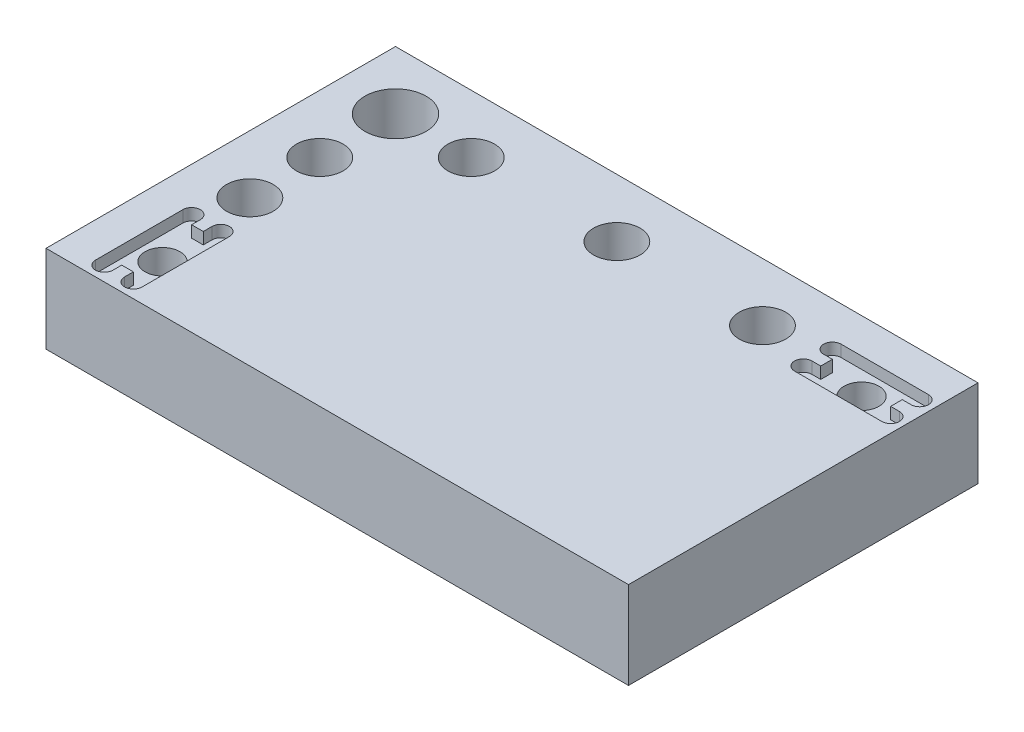
SolidWorks part; units mm, degrees
material "7075-T6, Plate (SS)"
ref_plane "Front Plane" through (0, 0, 0) normal (0, 0, 1) x (1, 0, 0)
ref_plane "Top Plane" through (0, 0, 0) normal (0, 1, 0) x (1, 0, 0)
ref_plane "Right Plane" through (0, 0, 0) normal (1, 0, 0) x (0, 0, -1)
sketch "Sketch1" plane through (0, 0, 0) normal (0, 1, 0) x (1, 0, 0)
  line L1 (-50, -30) -> (50, -30)
  line L2 (-50, -30) -> (-50, 30)
  line L3 (-50, 30) -> (50, 30)
  line L4 (50, -30) -> (50, 30)
  line L5 (-50, -30) -> (50, 30) construction
  line L6 (-50, 30) -> (50, -30) construction
  point P0 (0, 0)
  dimension "D1" = 100
  dimension "D2" = 60
extrude "Boss-Extrude1" add sketch "Sketch1" along normal blind 15
sketch "Sketch4" plane through (0, 15, 0) normal (0, 1, 0) x (1, 0, 0)
  line L0 (-50, 30) -> (-50, -30) construction
  line L1 (50, 30) -> (-50, 30) construction
  circle A0 centre (-40, 20) radius 3
  dimension "D3" = 6
  dimension "D1" = 10
  dimension "D2" = 10
extrude "Cut-Extrude1" cut sketch "Sketch4" against normal up to next
sketch "Sketch5" plane through (0, 15, 0) normal (0, 1, 0) x (1, 0, 0)
  circle A0 centre (-40, 20) radius 5.25
  dimension "D1" = 10.5
extrude "Cut-Extrude2" cut sketch "Sketch5" against normal blind 7.7
sketch "Sketch6" plane through (0, 15, 0) normal (0, 1, 0) x (1, 0, 0)
  line L0 (-50, 30) -> (-50, -30) construction
  line L1 (50, 30) -> (-50, 30) construction
  circle A0 centre (-40, 7) radius 4
  circle A1 centre (-40, -5) radius 4
  circle A2 centre (-27, 20) radius 4
  circle A3 centre (-2, 20) radius 4
  circle A4 centre (23, 20) radius 4
  dimension "D1" = 8
  dimension "D4" = 23
  dimension "D2" = 10
  dimension "D3" = 10
  dimension "D5" = 35
  dimension "D6" = 23
  dimension "D7" = 48
  dimension "D8" = 73
extrude "Cut-Extrude3" cut sketch "Sketch6" against normal up to next
sketch "Sketch7" plane through (0, 0, 0) normal (0, -1, 0) x (1, 0, 0)
  line L0 (-46, 5) -> (-34, 5) construction
  line L1 (-46, 6.5) -> (-34, 6.5)
  line L2 (-46, 3.5) -> (-34, 3.5)
  line L3 (-46, -7) -> (-34, -7) construction
  line L4 (-46, -5.5) -> (-34, -5.5)
  line L5 (-46, -8.5) -> (-34, -8.5)
  line L6 (-27, -26) -> (-27, -14) construction
  line L7 (-28.5, -26) -> (-28.5, -14)
  line L8 (-25.5, -26) -> (-25.5, -14)
  line L9 (-2, -26) -> (-2, -14) construction
  line L10 (-3.5, -26) -> (-3.5, -14)
  line L11 (-0.5, -26) -> (-0.5, -14)
  line L12 (23, -26) -> (23, -14) construction
  line L13 (21.5, -26) -> (21.5, -14)
  line L14 (24.5, -26) -> (24.5, -14)
  arc A0 (-46, 6.5) -> (-46, 3.5) centre (-46, 5) ccw
  arc A1 (-34, 3.5) -> (-34, 6.5) centre (-34, 5) ccw
  arc A2 (-46, -5.5) -> (-46, -8.5) centre (-46, -7) ccw
  arc A3 (-34, -8.5) -> (-34, -5.5) centre (-34, -7) ccw
  arc A4 (-28.5, -26) -> (-25.5, -26) centre (-27, -26) ccw
  arc A5 (-25.5, -14) -> (-28.5, -14) centre (-27, -14) ccw
  arc A6 (-3.5, -26) -> (-0.5, -26) centre (-2, -26) ccw
  arc A7 (-0.5, -14) -> (-3.5, -14) centre (-2, -14) ccw
  arc A8 (21.5, -26) -> (24.5, -26) centre (23, -26) ccw
  arc A9 (24.5, -14) -> (21.5, -14) centre (23, -14) ccw
  point P2 (-40, 5)
  point P9 (-40, -7)
  point P18 (-27, -20)
  point P25 (-2, -20)
  point P33 (23, -20)
  dimension "D1" = 12
  dimension "D2" = 3
extrude "Cut-Extrude4" cut sketch "Sketch7" against normal blind 4
sketch "Sketch8" plane through (0, 15, 0) normal (0, 1, 0) x (1, 0, 0)
  line L0 (-50, 30) -> (-50, -30) construction
  line L1 (50, 30) -> (-50, 30) construction
  circle A0 centre (40, 20) radius 3
  circle A1 centre (-40, -20) radius 3
  dimension "D3" = 6
  dimension "D1" = 90
  dimension "D2" = 50
  dimension "D4" = 10
  dimension "D5" = 10
extrude "Cut-Extrude5" cut sketch "Sketch8" against normal up to next
sketch "Sketch9" plane through (0, 15, 0) normal (0, 1, 0) x (1, 0, 0)
  line L0 (-37.5, -27.5) -> (-37.5, -12.5) construction
  line L3 (34, 17.5) -> (46, 17.5)
  line L4 (34, 17.5) -> (34, 22.5)
  line L5 (34, 22.5) -> (46, 22.5)
  line L6 (46, 17.5) -> (46, 22.5)
  line L7 (34, 17.5) -> (46, 22.5) construction
  line L8 (34, 22.5) -> (46, 17.5) construction
  line L9 (-42.5, -26) -> (-37.5, -26)
  line L10 (-42.5, -26) -> (-42.5, -14)
  line L11 (-42.5, -14) -> (-37.5, -14)
  line L12 (-37.5, -26) -> (-37.5, -14)
  line L13 (-42.5, -26) -> (-37.5, -14) construction
  line L14 (-42.5, -14) -> (-37.5, -26) construction
  line L15 (-39, -27.5) -> (-39, -12.5)
  line L16 (-36, -27.5) -> (-36, -12.5)
  line L17 (-42.5, -27.5) -> (-42.5, -12.5) construction
  line L18 (-44, -27.5) -> (-44, -12.5)
  line L19 (-41, -27.5) -> (-41, -12.5)
  line L20 (32.5, 22.5) -> (47.5, 22.5) construction
  line L21 (32.5, 24) -> (47.5, 24)
  line L22 (32.5, 21) -> (47.5, 21)
  line L23 (32.5, 17.5) -> (47.5, 17.5) construction
  line L24 (32.5, 19) -> (47.5, 19)
  line L25 (32.5, 16) -> (47.5, 16)
  arc A2 (-39, -27.5) -> (-36, -27.5) centre (-37.5, -27.5) ccw
  arc A3 (-36, -12.5) -> (-39, -12.5) centre (-37.5, -12.5) ccw
  arc A4 (-44, -27.5) -> (-41, -27.5) centre (-42.5, -27.5) ccw
  arc A5 (-41, -12.5) -> (-44, -12.5) centre (-42.5, -12.5) ccw
  arc A6 (32.5, 24) -> (32.5, 21) centre (32.5, 22.5) ccw
  arc A7 (47.5, 21) -> (47.5, 24) centre (47.5, 22.5) ccw
  arc A8 (32.5, 19) -> (32.5, 16) centre (32.5, 17.5) ccw
  arc A9 (47.5, 16) -> (47.5, 19) centre (47.5, 17.5) ccw
  point P0 (40, 20)
  point P5 (-40, -20)
  point P14 (-37.5, -20)
  point P20 (-42.5, -20)
  point P27 (40, 22.5)
  point P34 (40, 17.5)
  circle M18 centre (40, 20) radius 3
  circle M19 centre (-40, -20) radius 3
  dimension "D3" = 1.5
  dimension "D1" = 12
  dimension "D2" = 15
  dimension "D4" = 8
extrude "Cut-Extrude6" cut sketch "Sketch9" against normal blind 2 contours L19 A5 L18 A4 L9 L10 L11 M19 | L19 L15 L11 M19 | L9 L19 L10 M19 | L19 L9 L15 M19 | L15 L9 L12 M19 | L16 A3 L15 L11 L12 L9 A2 M19 | L15 L12 L11 M19 | L19 L11 L10 M19 | L24 L4 L3 M18 | L24 L3 L6 M18 | L25 A9 L24 L6 L3 L4 A8 M18 | L22 L6 L5 M18 | L24 L6 L22 M18 | L4 L24 L22 M18 | L4 L22 L5 M18 | L22 A7 L21 A6 L4 L5 L6 M18
hole_wizard "M3 Tapped Hole1" positions "Sketch10" profile "Sketch11" tap size "M3" standard "DIN"
sketch "Sketch10" plane through (0, 0, 0) normal (0, -1, 0) x (-1, 0, 0)
  line L0 (27.2236, -13.0815) -> (13.0815, -27.2236) construction
  line L1 (13.0815, -27.2236) -> (-27.2236, 13.0815) construction
  line L2 (-27.2236, 13.0815) -> (-13.0815, 27.2236) construction
  line L3 (-13.0815, 27.2236) -> (27.2236, -13.0815) construction
  line L5 (13.0815, -27.2236) -> (-13.0815, 27.2236) construction
  line L7 (-27.2236, 13.0815) -> (27.2236, -13.0815) construction
  line L9 (50, -30) -> (-50, -30) construction
  line L10 (50, 30) -> (50, -30) construction
  line L11 (-50, 30) -> (50, 30) construction
  point P4 (28.5, -18)
  point P6 (27.2236, -13.0815)
  point P8 (28.5, 2)
  point P10 (-27.7424, -18)
  point P12 (-27.7424, 2)
  point P14 (-27.2236, 13.0815)
  point P16 (-13.0815, 27.2236)
  point P20 (13.0815, -27.2236)
  point P43 (0, 0)
  dimension "D1" = 20
  dimension "D2" = 57
  dimension "D3" = 45
  dimension "D4" = 21.5
  dimension "D5" = 48
  dimension "D6" = 28
sketch "Sketch11" plane through (-28.5, 0, 18) normal (1, 0, 0) x (0, 0, -1)
  line L0 (0, 0) -> (0, 10.7511)
  line L1 (0, 10.7511) -> (1.25, 10)
  line L2 (1.25, 10) -> (1.25, 0)
  line L5 (1.25, 0) -> (0, 0)
  line L10 (0, 10.7511) -> (-1.25, 10) construction
  line L11 (0, -6.35) -> (0, 107.95) construction
  dimension "Tap Drill Dia." = 2.5
  dimension "Tap Drill Depth" = 10
  dimension "Drill Angle" = 118
cosmetic thread "Hole Thread1" parameters "D1"=7, "D2"=3
cosmetic thread "Hole Thread2" parameters "D1"=7, "D2"=3
cosmetic thread "Hole Thread3" parameters "D1"=7, "D2"=3
cosmetic thread "Hole Thread4" parameters "D1"=7, "D2"=3
cosmetic thread "Hole Thread5" parameters "D1"=7, "D2"=3
cosmetic thread "Hole Thread6" parameters "D1"=7, "D2"=3
cosmetic thread "Hole Thread7" parameters "D1"=7, "D2"=3
cosmetic thread "Hole Thread8" parameters "D1"=7, "D2"=3
